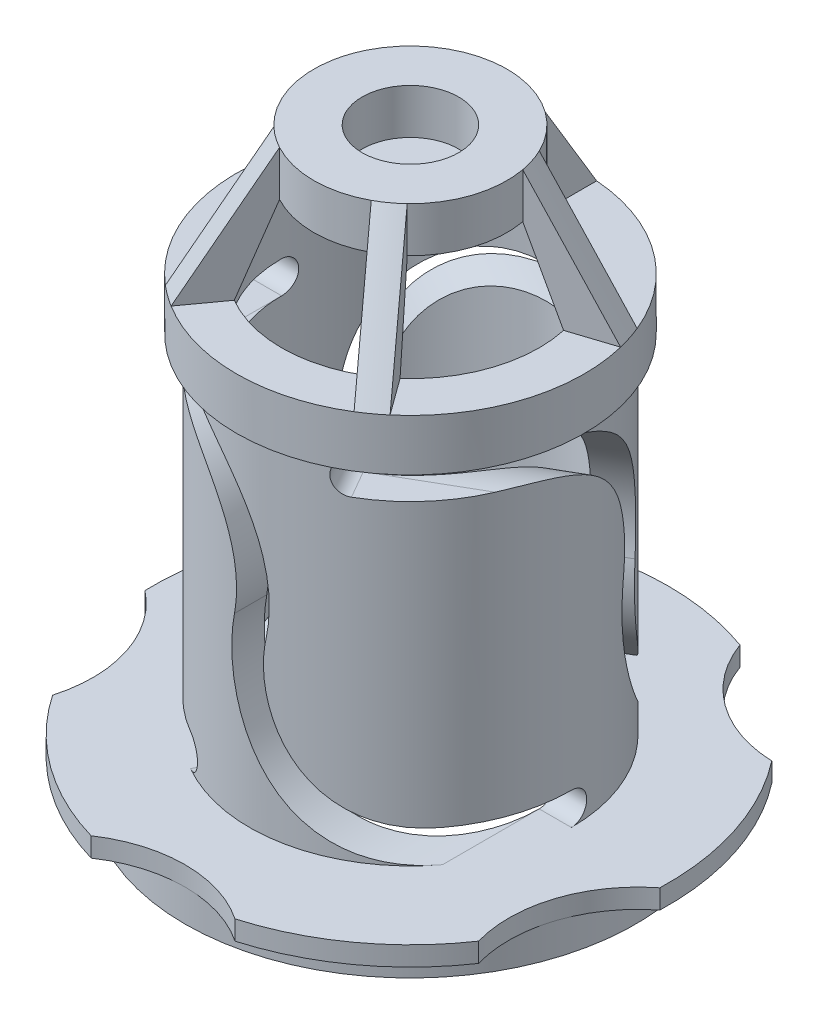
SolidWorks part; units mm, degrees
ref_plane "前视基准面" through (0, 0, 0) normal (0, 0, 1) x (1, 0, 0)
ref_plane "上视基准面" through (0, 0, 0) normal (0, 1, 0) x (1, 0, 0)
ref_plane "右视基准面" through (0, 0, 0) normal (1, 0, 0) x (0, 0, -1)
other "Configuration Table"
sketch "草图1" plane through (0, 0, 0) normal (0, 0, 1) x (1, 0, 0)
  line L0 (-32.2302, 0) -> (54.8921, 0) construction
  line L1 (0, 100.8102) -> (0, -31.286) construction
  line L2 (20, 0) -> (35, 0)
  line L3 (35, 0) -> (35, 5)
  line L4 (35, 5) -> (40, 5)
  line L5 (40, 5) -> (40, 8)
  line L6 (40, 8) -> (25, 8)
  line L7 (25, 8) -> (25, 62)
  line L8 (25, 62) -> (27, 62)
  line L9 (27, 62) -> (27, 70)
  line L10 (27, 70) -> (15, 90)
  line L11 (15, 90) -> (7.5, 90)
  line L12 (7.5, 90) -> (7.5, 83)
  line L13 (7.5, 83) -> (15, 83)
  line L14 (15, 83) -> (20, 70)
  line L15 (20, 70) -> (20, 0)
  point P5 (25, 35)
  point P17 (11.25, 83)
  point P19 (0, 100.8102)
  point P22 (20, 0)
  point P23 (0, 0)
  point P24 (11.9656, 83)
  point P25 (15, 83)
  point P26 (0, 0)
  dimension "D1" = 70
  dimension "D2" = 5
  dimension "D3" = 40
  dimension "D4" = 5
  dimension "D5" = 70
  dimension "D6" = 3
  dimension "D7" = 5
  dimension "D8" = 2
  dimension "D9" = 8
  dimension "D10" = 7
  dimension "D11" = 15
  dimension "D12" = 30
  dimension "D13" = 90
revolve "旋转1" add sketch "草图1" angle 360 about L1
sketch "草图4" plane through (0, 90, 0) normal (0, 1, 0) x (1, 0, 0)
  line L0 (-51.5767, 0) -> (56.9376, 0) construction
  line L6 (0, 50.0586) -> (0, -57.9265) construction
  line L7 (-25.6785, 8.3435) -> (0, 0) construction
  line L8 (0, 27) -> (-2, 25.5469)
  line L9 (-25.6785, 8.3435) -> (-15.8702, -21.8435)
  line L10 (-15.8702, -21.8435) -> (15.8702, -21.8435)
  line L11 (15.8702, -21.8435) -> (25.6785, 8.3435)
  line L12 (25.6785, 8.3435) -> (0, 27)
  line L13 (-2, 26.9258) -> (-2, -57.9265)
  line L14 (-25.0605, 10.2456) -> (0.618, 1.9021)
  line L15 (-23.6785, 9.7965) -> (-25.6785, 8.3435)
  line L16 (-2, 50.0586) -> (-2, -57.9265) construction
  circle A0 centre (0, 0) radius 27 construction
  circle A1 centre (0, 0) radius 27 construction
  circle A2 centre (0, 0) radius 27
  circle M2 centre (0, 0) radius 15
  dimension "D1" = 2
  dimension "D2" = 2
extrude "切除-拉伸4" cut sketch "草图4" against normal blind 20 contours L13 A2 L14 M2
sketch "草图5" plane through (0, 90, 0) normal (0, 1, 0) x (1, 0, 0)
  line L0 (-61.896, 0) -> (62.8005, 0) construction
  line L1 (0, 0) -> (0, -62.6058) construction
  circle A1 centre (0, 0) radius 40 construction
  circle A2 centre (0, 0) radius 40
  arc A6 (11.1688, -38.4091) -> (-11.1688, -38.4091) centre (0, -55) ccw
  circle A7 centre (0, 0) radius 35 construction
  point P3 (0, 0)
  dimension "D1" = 20
extrude "切除-拉伸5" cut sketch "草图5" against normal blind 101 contours A2 A6
pattern_circular "阵列(圆周)1" count 5 over 360 about axis through (0, 0, 0) along (0, 1, 0) of "切除-拉伸4", "切除-拉伸5"
sketch "草图7" plane through (0, 0, 0) normal (0, 0, 1) x (1, 0, 0)
  line L1 (-20, 62) -> (-25, 62)
  line L2 (-20, 70) -> (-20, 0) construction
  line L3 (-27, 62) -> (27, 62) construction
  line L4 (-25, 62) -> (25, 62) construction
  line L5 (20, 0) -> (20, 70) construction
  line L6 (-25, 62) -> (-25, 8) construction
  line L7 (-25, 62) -> (-25, 57)
  line L8 (33.0779, 8) -> (11.1688, 8) construction
  line L9 (-25, 57) -> (-20, 57)
  line L10 (20, 13) -> (25, 13)
  line L11 (25, 8) -> (25, 62) construction
  line L12 (25, 13) -> (25, 8)
  line L13 (25, 8) -> (20, 8)
  arc A0 (-20, 62) -> (2.4494, 34.4995) centre (-20, 39.0867) cw
  arc A1 (-20, 57) -> (-2.4494, 35.5005) centre (-20, 39.0867) cw
  arc A2 (20, 8) -> (-2.4494, 35.5005) centre (20, 30.9133) cw
  arc A3 (20, 13) -> (2.4494, 34.4995) centre (20, 30.9133) cw
  arc A4 (-20, 62) -> (-0.6666, 51.3845) centre (-20, 39.0867) cw construction
  arc A5 (-20, 57) -> (-4.8854, 48.701) centre (-20, 39.0867) cw construction
  dimension "D1" = 5
  dimension "D2" = 5
extrude "切除-拉伸6" cut sketch "草图7" along normal blind 101
sketch "草图8" plane through (0, 0, 0) normal (1, 0, 0) x (0, 0, -1)
  line L0 (0, 8) -> (0, 13) construction
  circle A0 centre (0, 10.5) radius 2.5
extrude "切除-拉伸7" cut sketch "草图8" along normal blind 101
sketch "草图9" plane through (0, 0, 0) normal (1, 0, 0) x (0, 0, -1)
  line L0 (0, 62) -> (0, 57) construction
  circle A1 centre (0, 59.5) radius 2.5
extrude "切除-拉伸8" cut sketch "草图9" against normal blind 101
pattern_circular "阵列(圆周)2" count 3 over 360 about axis through (0, 100.8102, 0) along (0, 1, 0) of "切除-拉伸6", "切除-拉伸7", "切除-拉伸8"
sketch "草图10" plane through (0, 0, 0) normal (0, -1, 0) x (1, 0, 0)
  line L0 (-46.2542, 0) -> (61.5296, 0) construction
  line L1 (0, 43.4337) -> (0, -66.0681) construction
  line L3 (0, -33.3738) -> (31.7404, -10.3131)
  line L4 (31.7404, -10.3131) -> (19.6166, 27)
  line L5 (19.6166, 27) -> (-19.6166, 27)
  line L6 (-19.6166, 27) -> (-31.7404, -10.3131)
  line L7 (-31.7404, -10.3131) -> (0, -33.3738)
  circle A0 centre (0, 0) radius 27 construction
  circle A1 centre (0, 0) radius 20 construction
  dimension "D1" = 7
extrude "切除-拉伸9" cut sketch "草图10" against normal blind 5 draft 30
